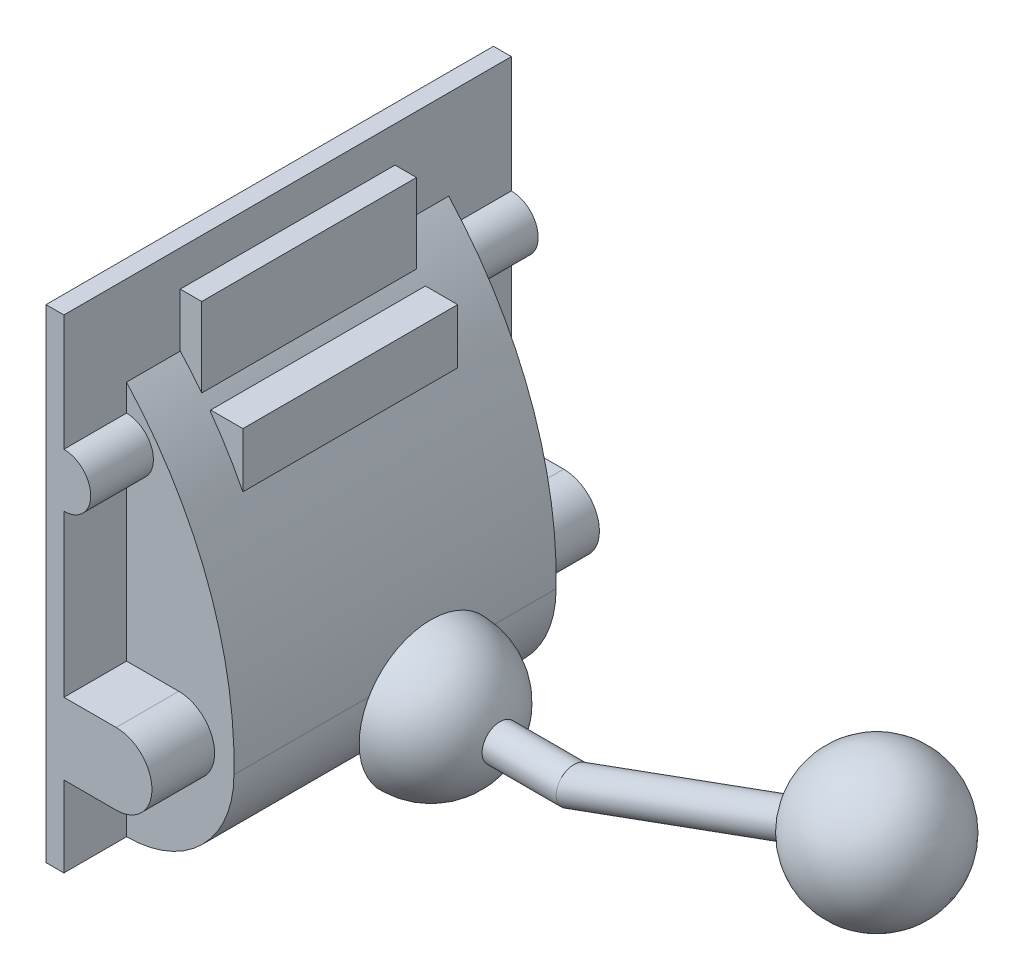
SolidWorks part; units mm, degrees
ref_plane "Front Plane" through (0, 0, 0) normal (0, 0, 1) x (1, 0, 0)
ref_plane "Top Plane" through (0, 0, 0) normal (0, 1, 0) x (1, 0, 0)
ref_plane "Right Plane" through (0, 0, 0) normal (1, 0, 0) x (0, 0, -1)
sketch "Sketch1" plane through (0, 0, 0) normal (0, 0, 1) x (1, 0, 0)
  line L0 (0, 0) -> (0, 220)
  arc A0 (0, 0) -> (60, 60) centre (0, 60) ccw
  arc A1 (0, 220) -> (60, 60) centre (-169.9452, 65.0206) cw
  dimension "D2" = 60
  dimension "D3" = 230
  dimension "D1" = 220
extrude "Boss-Extrude1" add sketch "Sketch1" along normal mid plane 180
sketch "Sketch2" plane through (0, 0, 0) normal (-1, 0, 0) x (0, 0, 1)
  line L1 (-125, 0) -> (125, 0)
  line L2 (-125, 0) -> (-125, 270)
  line L3 (-125, 270) -> (125, 270)
  line L4 (125, 0) -> (125, 270)
  dimension "D1" = 270
  dimension "D2" = 250
extrude "Boss-Extrude2" add sketch "Sketch2" along normal blind 10
sketch "Sketch4" plane through (0, 0, 0) normal (0, 0, 1) x (1, 0, 0)
  line L0 (0, 0) -> (0, 270) construction
  line L1 (0, 250) -> (12, 250)
  line L2 (0, 250) -> (0, 177.0703)
  line L3 (0, 177.0703) -> (12, 177.0703)
  line L4 (12, 250) -> (12, 177.0703)
  line L6 (17, 200) -> (35, 200)
  line L7 (17, 200) -> (17, 137.3662)
  line L8 (17, 137.3662) -> (35, 137.3662)
  line L9 (35, 200) -> (35, 137.3662)
  dimension "D1" = 12
  dimension "D2" = 18
  dimension "D3" = 30
  dimension "D4" = 50
  dimension "D5" = 35
extrude "Boss-Extrude3" add sketch "Sketch4" along normal mid plane 120
sketch "Sketch5" plane through (0, 0, 125) normal (0, 0, 1) x (1, 0, 0)
  line L0 (0, 220) -> (0, 0) construction
  line L1 (0, 85) -> (29.1951, 85)
  line L2 (0, 85) -> (0, 45)
  line L3 (0, 45) -> (29.1951, 45)
  line L4 (29.1951, 85) -> (29.1951, 45) construction
  line L5 (0, 250) -> (0, 220) construction
  line L6 (0, 0) -> (0, 270) construction
  line L7 (12, 250) -> (0, 250) construction
  line L8 (0, 205) -> (0, 175)
  arc A0 (29.1951, 85) -> (29.1951, 45) centre (29.1951, 65) cw
  arc A1 (0, 205) -> (0, 175) centre (0, 190) cw
  dimension "D2" = 20
  dimension "D4" = 15
  dimension "D1" = 65
  dimension "D3" = 60
extrude "Boss-Extrude4" add sketch "Sketch5" against normal up to surface (250 mm away) up to face at (-5, 135, -125)
sketch "Sketch6" plane through (0, 0, 0) normal (1, 0, 0) x (0, 0, -1)
  line L0 (-90, 60) -> (90, 60) construction
  circle A0 centre (0, 60) radius 10
  dimension "D1" = 20
extrude "Boss-Extrude5" add sketch "Sketch6" along normal blind 160
ref_plane "Plane1" through (0, 60, 0) normal (0, -1, 0) x (-1, 0, 0)
sketch "Sketch7" plane through (0, 60, 0) normal (0, -1, 0) x (-1, 0, 0)
  line L0 (-80, 0) -> (-80, -40)
  line L1 (-120, 0) -> (-80, 0)
  line L2 (-160, 10) -> (-160, -10) construction
  arc A0 (-80, -40) -> (-120, 0) centre (-80, 0) cw
  point P5 (0, 0)
  dimension "D1" = 40
  dimension "D2" = 80
revolve "Revolve1" add sketch "Sketch7" angle 360 about L1
sketch "Sketch8" plane through (0, 0, 0) normal (0, 0, 1) x (1, 0, 0)
  line L0 (160, 60) -> (329.1447, 121.5636)
  line L1 (160, 50) -> (160, 70) construction
  line L2 (59.1608, 50) -> (160, 50) construction
  dimension "D1" = 180
  dimension "D2" = 20
sketch "Sketch9" plane through (160, 0, 0) normal (1, 0, 0) x (0, 0, -1)
  circle A1 centre (0, 60) radius 10
  circle A2 centre (0, 60) radius 10
  dimension "D1" = 0
sweep "Sweep1" add profiles "Sketch9" path "Sketch8"
sketch "Sketch10" plane through (0, 0, 0) normal (0, 0, 1) x (1, 0, 0)
  line L0 (329.1447, 111.5636) -> (329.1447, 131.5636) construction
  line L1 (329.1447, 161.5636) -> (329.1447, 81.5636)
  arc A0 (329.1447, 161.5636) -> (329.1447, 81.5636) centre (329.1447, 121.5636) cw
  dimension "D1" = 80
revolve "Revolve2" add sketch "Sketch10" angle 360 about L1
